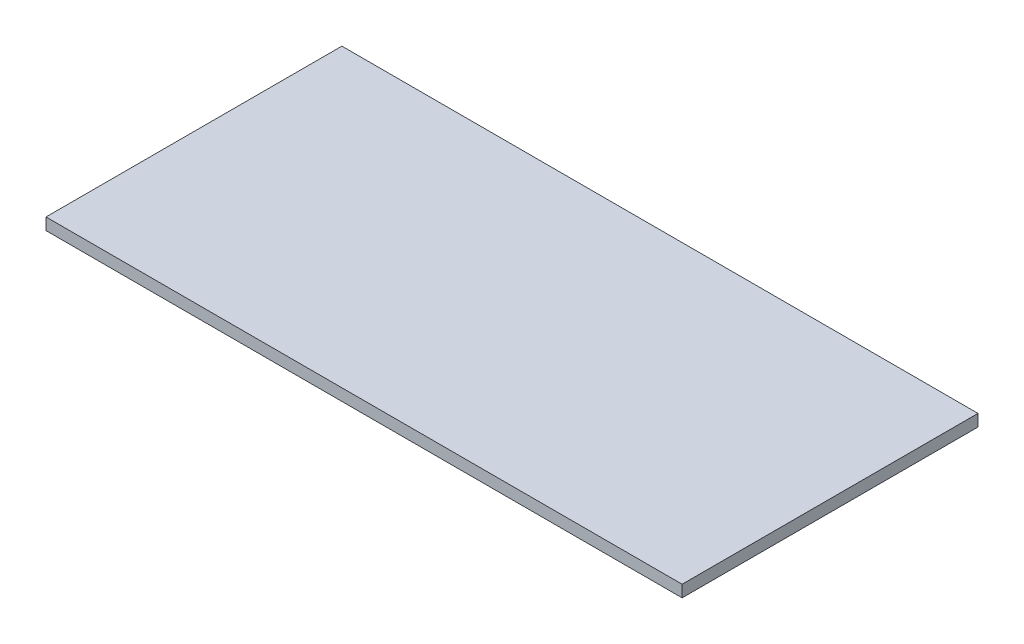
SolidWorks part; units mm, degrees
material "7079 Alloy"
ref_plane "Front Plane" through (0, 0, 0) normal (0, 0, 1) x (1, 0, 0)
ref_plane "Top Plane" through (0, 0, 0) normal (0, 1, 0) x (1, 0, 0)
ref_plane "Right Plane" through (0, 0, 0) normal (1, 0, 0) x (0, 0, -1)
sketch "Sketch1" plane through (0, 0, 0) normal (0, 1, 0) x (1, 0, 0)
  line L1 (0, 0) -> (430, 0)
  line L2 (0, 0) -> (0, 200)
  line L3 (0, 200) -> (430, 200)
  line L4 (430, 0) -> (430, 200)
extrude "Extrude1" add sketch "Sketch1" along normal blind 8
